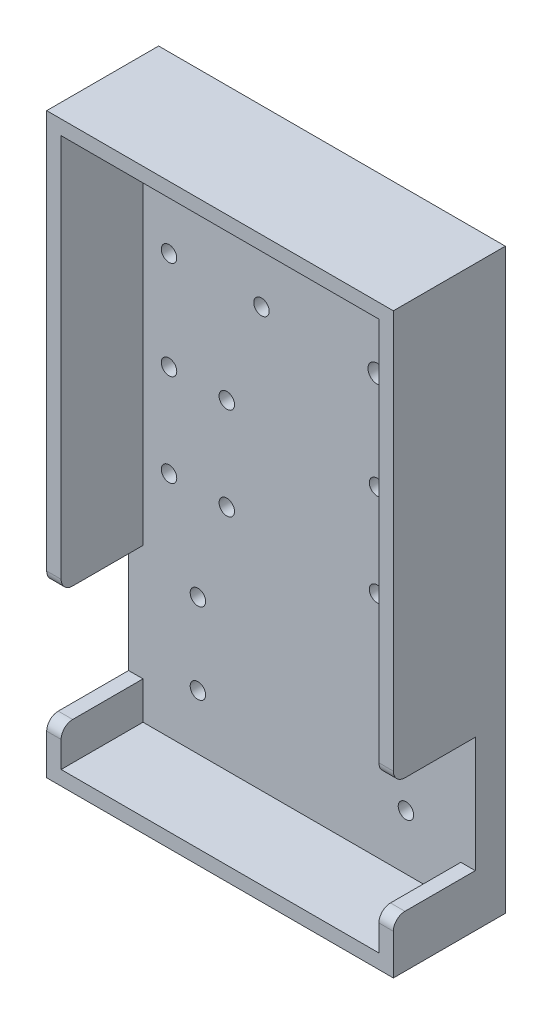
SolidWorks part; units mm, degrees
ref_plane "Front Plane" through (0, 0, 0) normal (1, 0, 0) x (0, 1, 0)
ref_plane "Top Plane" through (0, 0, 0) normal (0, 0, 1) x (0, 1, 0)
ref_plane "Right Plane" through (0, 0, 0) normal (0, 1, 0) x (-1, 0, 0)
sketch "Sketch1" plane through (0, 0, 0) normal (0, 0, 1) x (0, 1, 0)
  line L1 (0, 0) -> (127, 0)
  line L2 (0, 0) -> (0, -76.2)
  line L3 (0, -76.2) -> (127, -76.2)
  line L4 (127, 0) -> (127, -76.2)
  dimension "D1" = 127
  dimension "D2" = 76.2
extrude "Boss-Extrude1" add sketch "Sketch1" along normal blind 6.604
sketch "Sketch2" plane through (0, 0, 6.604) normal (0, 0, 1) x (1, 0, 0)
  line L0 (15.24, 15.24) -> (60.96, 15.24) construction
  line L1 (12.7, 12.7) -> (63.5, 12.7) construction
  line L2 (12.7, 12.7) -> (12.7, 35.56) construction
  line L3 (12.7, 35.56) -> (63.5, 35.56) construction
  line L4 (63.5, 12.7) -> (63.5, 35.56) construction
  line L5 (6.35, 50.8) -> (24.13, 50.8) construction
  line L6 (6.35, 50.8) -> (6.35, 76.2) construction
  line L7 (6.35, 76.2) -> (24.13, 76.2) construction
  line L8 (24.13, 50.8) -> (24.13, 76.2) construction
  line L9 (6.35, 92.71) -> (31.75, 92.71) construction
  line L10 (6.35, 92.71) -> (6.35, 118.11) construction
  line L11 (6.35, 118.11) -> (31.75, 118.11) construction
  line L12 (31.75, 92.71) -> (31.75, 118.11) construction
  line L13 (52.07, 50.8) -> (69.85, 50.8) construction
  line L14 (52.07, 50.8) -> (52.07, 76.2) construction
  line L15 (52.07, 76.2) -> (69.85, 76.2) construction
  line L16 (69.85, 50.8) -> (69.85, 76.2) construction
  line L21 (60.96, 15.24) -> (60.96, 33.02) construction
  line L22 (15.24, 33.02) -> (60.96, 33.02) construction
  line L23 (15.24, 15.24) -> (15.24, 33.02) construction
  line L24 (8.89, 53.34) -> (21.59, 53.34) construction
  line L25 (21.59, 53.34) -> (21.59, 73.66) construction
  line L26 (8.89, 73.66) -> (21.59, 73.66) construction
  line L27 (8.89, 53.34) -> (8.89, 73.66) construction
  line L28 (8.89, 95.25) -> (29.21, 95.25) construction
  line L29 (29.21, 95.25) -> (29.21, 115.57) construction
  line L30 (8.89, 115.57) -> (29.21, 115.57) construction
  line L31 (8.89, 95.25) -> (8.89, 115.57) construction
  line L32 (54.61, 53.34) -> (67.31, 53.34) construction
  line L33 (67.31, 53.34) -> (67.31, 73.66) construction
  line L34 (54.61, 73.66) -> (67.31, 73.66) construction
  line L35 (54.61, 53.34) -> (54.61, 73.66) construction
  line L40 (0, 0) -> (76.2, 0) construction
  line L41 (76.2, 0) -> (76.2, 127) construction
  line L42 (76.2, 127) -> (0, 127) construction
  line L43 (0, 127) -> (0, 0) construction
  point P20 (15.24, 15.24)
  point P21 (60.96, 15.24)
  point P22 (60.96, 33.02)
  point P23 (15.24, 33.02)
  point P24 (8.89, 53.34)
  point P25 (21.59, 53.34)
  point P26 (21.59, 73.66)
  point P27 (8.89, 73.66)
  point P28 (8.89, 95.25)
  point P29 (29.21, 95.25)
  point P30 (29.21, 115.57)
  point P31 (8.89, 115.57)
  point P32 (54.61, 53.34)
  point P33 (67.31, 53.34)
  point P34 (67.31, 73.66)
  point P35 (54.61, 73.66)
  dimension "D2" = 22.86
  dimension "D3" = 50.8
  dimension "D4" = 25.4
  dimension "D5" = 17.78
  dimension "D6" = 17.78
  dimension "D7" = 25.4
  dimension "D8" = 25.4
  dimension "D9" = 25.4
  dimension "D12" = 12.7
  dimension "D13" = 12.7
  dimension "D15" = 8.89
  dimension "0.75" = 6.35
  dimension "D17" = 6.35
  dimension "D18" = 6.35
  dimension "D19" = 50.8
  dimension "D20" = 50.8
  dimension "D1" = 2.54
sketch "Sketch9" plane through (0, 0, 6.604) normal (0, 0, 1) x (1, 0, 0)
  line L10 (54.61, 115.57) -> (54.61, 95.25) construction
  line L11 (52.07, 118.11) -> (69.85, 118.11) construction
  line L12 (52.07, 118.11) -> (52.07, 92.71) construction
  line L13 (52.07, 92.71) -> (69.85, 92.71) construction
  line L14 (69.85, 118.11) -> (69.85, 92.71) construction
  line L15 (54.61, 95.25) -> (67.31, 95.25) construction
  line L16 (67.31, 115.57) -> (67.31, 95.25) construction
  line L17 (54.61, 115.57) -> (67.31, 115.57) construction
  line L18 (76.2, 127) -> (0, 127) construction
  line L19 (76.2, 0) -> (76.2, 127) construction
  point P4 (54.61, 115.57)
  point P5 (54.61, 95.25)
  point P6 (67.31, 95.25)
  point P7 (67.31, 115.57)
  dimension "D1" = 2.54
  dimension "D2" = 8.89
  dimension "D3" = 6.35
  dimension "D4" = 17.78
  dimension "D5" = 25.4
hole_wizard "Hole2" positions "Sketch2" profile "Sketch10" legacy
sketch "Sketch10" plane through (54.61, 73.66, 6.604) normal (1, 0, 0) x (0, -1, 0)
  line L0 (0, 0) -> (0, 7)
  line L1 (0, 7) -> (1.7, 7)
  line L2 (1.7, 7) -> (1.7, 0)
  line L3 (1.7, 0) -> (0, 0)
  line L4 (0, 110) -> (0, -10) construction
  dimension "Diameter" = 3.4
  dimension "Depth" = 7
hole_wizard "Hole3" positions "Sketch9" profile "Sketch11" legacy
sketch "Sketch11" plane through (67.31, 115.57, 6.604) normal (1, 0, 0) x (0, -1, 0)
  line L0 (0, 0) -> (0, 7)
  line L1 (0, 7) -> (2, 7)
  line L2 (2, 7) -> (2, 0)
  line L3 (2, 0) -> (0, 0)
  line L4 (0, 110) -> (0, -10) construction
  dimension "Diameter" = 4
  dimension "Depth" = 7
sketch "Sketch12" plane through (0, 0, 6.604) normal (0, 0, 1) x (1, 0, 0)
  line L0 (3.175, 123.825) -> (3.175, 36.83)
  line L1 (0, 127) -> (76.2, 127)
  line L2 (0, 127) -> (0, 36.83)
  line L3 (0, 0) -> (76.2, 0)
  line L4 (76.2, 127) -> (76.2, 36.83)
  line L5 (3.175, 3.175) -> (73.025, 3.175)
  line L6 (73.025, 123.825) -> (73.025, 36.83)
  line L7 (3.175, 123.825) -> (73.025, 123.825)
  line L10 (73.025, 123.825) -> (73.025, 3.175) construction
  line L12 (76.2, 127) -> (76.2, 0) construction
  line L13 (60.96, 33.02) -> (60.96, 15.24) construction
  line L14 (0, 36.83) -> (3.175, 36.83)
  line L15 (73.025, 36.83) -> (76.2, 36.83)
  line L16 (73.025, 11.43) -> (76.2, 11.43)
  line L17 (-939.04, 24.13) -> (49060.96, 24.13) construction
  line L18 (0, 11.43) -> (3.175, 11.43)
  line L19 (3.175, 11.43) -> (3.175, 3.175)
  line L20 (3.175, 123.825) -> (3.175, 3.175) construction
  line L21 (0, 11.43) -> (0, 0)
  line L22 (0, 127) -> (0, 0) construction
  line L23 (73.025, 11.43) -> (73.025, 3.175)
  line L24 (76.2, 11.43) -> (76.2, 0)
  circle A2 centre (60.96, 15.24) radius 1.7 construction
  circle A3 centre (60.96, 15.24) radius 1.7 construction
  circle A4 centre (60.96, 33.02) radius 1.7 construction
  circle A5 centre (60.96, 33.02) radius 1.7 construction
  point P24 (60.96, 24.13)
  dimension "D2" = 12.7
  dimension "0.5" = 12.7
  dimension "D3" = 12.7
  dimension "D4" = 12.7
  dimension "D1" = 3.175
extrude "Boss-Extrude2" add sketch "Sketch12" along normal blind 18
fillet "Fillet1" radius 2.54 4 edges at (74.6125, 11.43, 24.604) (1.5875, 11.43, 24.604) (1.5875, 36.83, 24.604) (74.6125, 36.83, 24.604)
equation "\"LENGTH\" = 5in"
equation "\"WIDTH\" = 3in"
equation "\"D1@Sketch1\"=\"LENGTH\""
equation "\"D2@Sketch1\"=\"WIDTH\""
equation "\"D19@Sketch2\"=\"LENGTH\"/2-0.5"
equation "\"D20@Sketch2\"=\"LENGTH\"/2-0.5"
